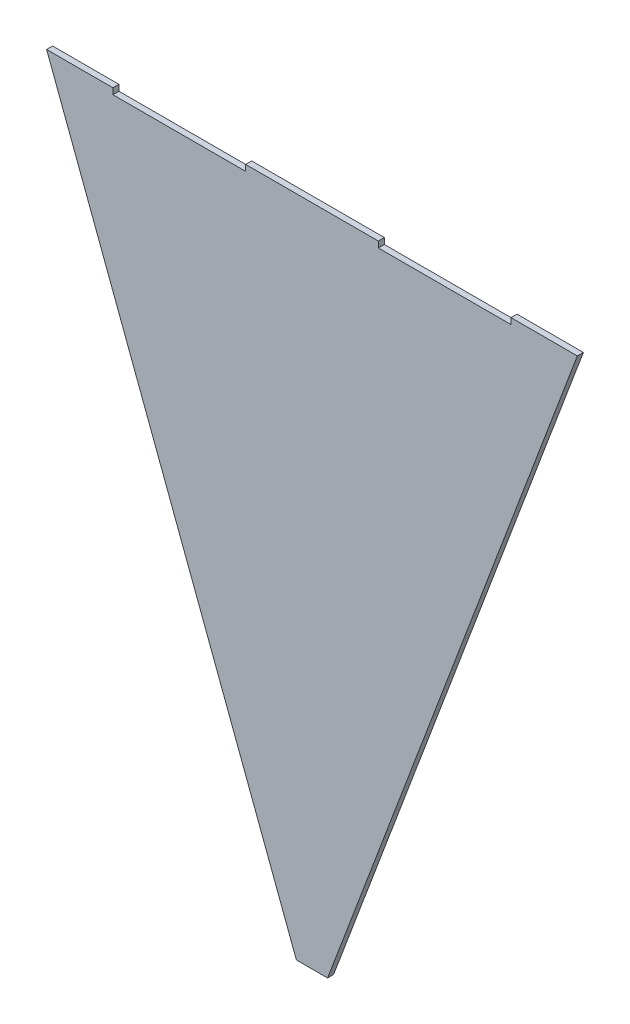
SolidWorks part; units mm, degrees
ref_plane "Plano frontal" through (0, 0, 0) normal (0, 0, 1) x (1, 0, 0)
ref_plane "Plano superior" through (0, 0, 0) normal (0, 1, 0) x (1, 0, 0)
ref_plane "Plano direito" through (0, 0, 0) normal (1, 0, 0) x (0, 0, -1)
sketch "Esboço1" plane through (0, 0, 0) normal (0, 0, 1) x (1, 0, 0)
  line L0 (10.3553, 0) -> (176.0411, 440.2156) construction
  line L1 (176.0411, 440.2156) -> (10.3553, 0)
  line L2 (10.3553, 0) -> (-10.3553, 0)
  line L3 (-10.3553, 0) -> (-176.0404, 440.2156)
  line L4 (-176.0404, 440.2156) -> (-10.3553, 0) construction
  line L5 (-176.0404, 440.2156) -> (-132.0302, 440.2156)
  line L6 (-132.0302, 440.2156) -> (-132.0302, 436.2156)
  line L7 (-132.0302, 436.2156) -> (-44.0098, 436.2156)
  line L8 (-44.0098, 436.2156) -> (-44.0098, 440.2156)
  line L9 (132.0302, 436.2156) -> (132.0302, 440.2156)
  line L10 (44.0098, 436.2156) -> (132.0302, 436.2156)
  line L11 (44.0098, 440.2156) -> (44.0098, 436.2156)
  line L12 (132.0302, 440.2156) -> (176.0411, 440.2156)
  line L13 (-44.0098, 440.2156) -> (44.0098, 440.2156)
  point P2 (0, 0)
  point P12 (0, 440.2156)
  dimension "D1" = 20.7107
  dimension "D2" = 41.25
  dimension "D3" = 352.0815
  dimension "D4" = 44.0102
  dimension "D5" = 88.0204
  dimension "D6" = 4
  dimension "D7" = 88.0196
extrude "Ressalto-extrusão1" add sketch "Esboço1" along normal blind 4
